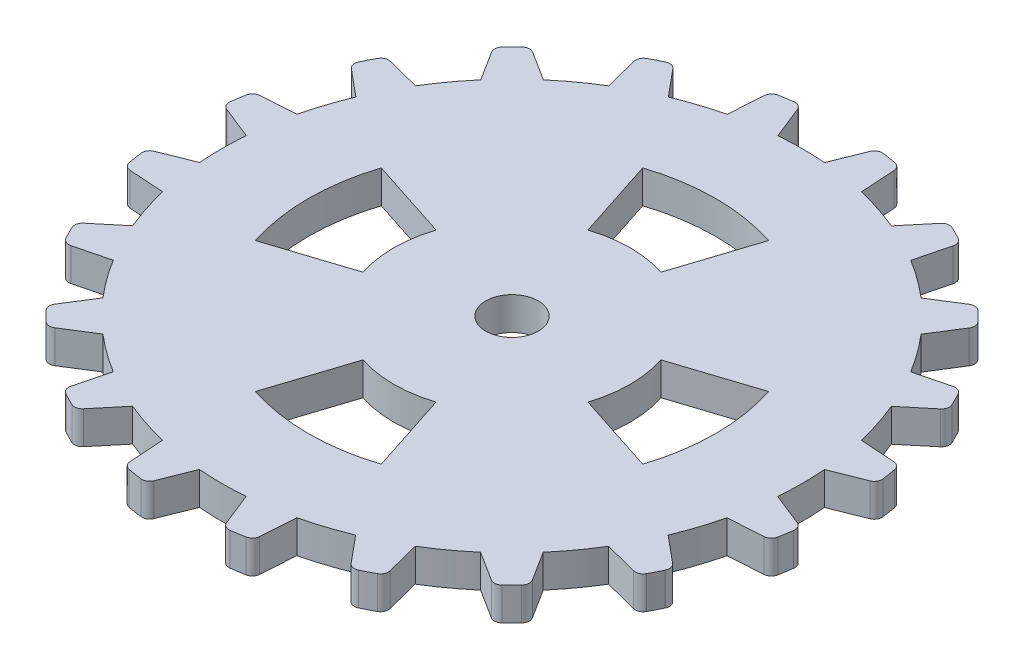
SolidWorks part; units mm, degrees
ref_plane "Front Plane" through (0, 0, 0) normal (0, 0, 1) x (1, 0, 0)
ref_plane "Top Plane" through (0, 0, 0) normal (0, 1, 0) x (1, 0, 0)
ref_plane "Right Plane" through (0, 0, 0) normal (1, 0, 0) x (0, 0, -1)
sketch "Sketch1" plane through (0, 0, 0) normal (0, 1, 0) x (1, 0, 0)
  line L0 (0, 0) -> (0, 28.8903) construction
  line L1 (-2.9264, 24.9115) -> (0, 0)
  line L2 (2.9395, 24.91) -> (0, 0)
  line L3 (-2.9264, 24.9115) -> (-1.7724, 22.0116)
  line L4 (2.9395, 24.91) -> (1.7839, 22.0106)
  line L5 (4.9149, 24.5966) -> (5.1163, 21.4819)
  line L6 (10.4932, 22.7824) -> (8.4983, 20.3821)
  line L7 (12.2751, 21.8739) -> (11.5042, 18.8495)
  line L8 (17.0198, 18.4248) -> (14.3807, 16.7584)
  line L9 (18.4337, 17.0101) -> (16.7659, 14.372)
  line L10 (21.8804, 12.2636) -> (18.8555, 11.4943)
  line L11 (22.7879, 10.4813) -> (20.3865, 8.4876)
  line L12 (24.5991, 4.902) -> (21.4846, 5.105)
  line L13 (24.9115, 2.9264) -> (22.0116, 1.7724)
  line L14 (24.91, -2.9395) -> (22.0106, -1.7839)
  line L15 (24.5966, -4.9149) -> (21.4819, -5.1163)
  line L16 (22.7824, -10.4932) -> (20.3821, -8.4983)
  line L17 (21.8739, -12.2751) -> (18.8495, -11.5042)
  line L18 (18.4248, -17.0198) -> (16.7584, -14.3807)
  line L19 (17.0101, -18.4337) -> (14.372, -16.7659)
  line L20 (12.2636, -21.8804) -> (11.4943, -18.8555)
  line L21 (10.4813, -22.7879) -> (8.4876, -20.3865)
  line L22 (4.902, -24.5991) -> (5.105, -21.4846)
  line L23 (2.9264, -24.9115) -> (1.7724, -22.0116)
  line L24 (-2.9395, -24.91) -> (-1.7839, -22.0106)
  line L25 (-4.9149, -24.5966) -> (-5.1163, -21.4819)
  line L26 (-10.4932, -22.7824) -> (-8.4983, -20.3821)
  line L27 (-12.2751, -21.8739) -> (-11.5042, -18.8495)
  line L28 (-17.0198, -18.4248) -> (-14.3807, -16.7584)
  line L29 (-18.4337, -17.0101) -> (-16.7659, -14.372)
  line L30 (-21.8804, -12.2636) -> (-18.8555, -11.4943)
  line L31 (-22.7879, -10.4813) -> (-20.3865, -8.4876)
  line L32 (-24.5991, -4.902) -> (-21.4846, -5.105)
  line L33 (-24.9115, -2.9264) -> (-22.0116, -1.7724)
  line L34 (-24.91, 2.9395) -> (-22.0106, 1.7839)
  line L35 (-24.5966, 4.9149) -> (-21.4819, 5.1163)
  line L36 (-22.7824, 10.4932) -> (-20.3821, 8.4983)
  line L37 (-21.8739, 12.2751) -> (-18.8495, 11.5042)
  line L38 (-18.4248, 17.0198) -> (-16.7584, 14.3807)
  line L39 (-17.0101, 18.4337) -> (-14.372, 16.7659)
  line L40 (-12.2636, 21.8804) -> (-11.4943, 18.8555)
  line L41 (-10.4813, 22.7879) -> (-8.4876, 20.3865)
  line L42 (-4.902, 24.5991) -> (-5.105, 21.4846)
  line L43 (4.7898, 14.7414) -> (2.7812, 8.5595)
  line L44 (-4.7898, 14.7414) -> (-2.7812, 8.5595)
  line L45 (14.7414, -4.7898) -> (8.5595, -2.7812)
  line L46 (14.7414, 4.7898) -> (8.5595, 2.7812)
  line L47 (-4.7898, -14.7414) -> (-2.7812, -8.5595)
  line L48 (4.7898, -14.7414) -> (2.7812, -8.5595)
  line L49 (-14.7414, 4.7898) -> (-8.5595, 2.7812)
  line L50 (-14.7414, -4.7898) -> (-8.5595, -2.7812)
  circle A0 centre (0, 0) radius 25.0828
  circle A1 centre (0, 0) radius 22.0828
  circle A2 centre (0, 0) radius 9
  circle A3 centre (0, 0) radius 15.5
  point P4 (-2.9264, 24.9115)
  point P7 (2.9395, 24.91)
  point P9 (-1.7724, 22.0116)
  point P13 (0, 22.0828)
  point P92 (0, 0)
  point P111 (0, 0)
  dimension "D1" = 50.1656
  dimension "D2" = 44.1656
  dimension "D8" = 18
  dimension "D9" = 31
  dimension "D3" = 13.43
  dimension "D4" = 6.7
  dimension "D5" = 15
  dimension "D6" = 15
  dimension "D10" = 18
  dimension "D11" = 18
  dimension "D7" = 20
  dimension "D12" = 4
extrude "Boss-Extrude1" add sketch "Sketch1" against normal blind 2.5 contours A1 L2 L1 | A1 L41 A0 L40 | A1 L1 A0 L42 | A1 L3 L1 | A1 L2 L4 | A1 L5 A0 L2 | A1 L7 A0 L6 | A1 L9 A0 L8 | A1 L11 A0 L10 | A1 L13 A0 L12 | L0 L2 A1 | L1 L0 A1 | A1 L15 A0 L14 | A1 L17 A0 L16 | A1 L19 A0 L18 | A1 L21 A0 L20 | A1 L23 A0 L22 | A1 L25 A0 L24 | A1 L27 A0 L26 | A1 L29 A0 L28 | A1 L31 A0 L30 | A1 L33 A0 L32 | A1 L39 A0 L38 | A1 L37 A0 L36 | A1 L35 A0 L34 | A3
fillet "Fillet1" radius 0.6 40 edges at (-10.4813, -1.25, -22.7879) (-17.0101, -1.25, -18.4337) (-24.91, -1.25, -2.9395) (-12.2636, -1.25, -21.8804) (-18.4248, -1.25, -17.0198) (-21.8739, -1.25, -12.2751) (-22.7824, -1.25, -10.4932) (-24.5966, -1.25, -4.9149) (-24.9115, -1.25, 2.9264) (-22.7879, -1.25, 10.4813) (-18.4337, -1.25, 17.0101) (-24.5991, -1.25, 4.902) (-21.8804, -1.25, 12.2636) (-17.0198, -1.25, 18.4248) (-12.2751, -1.25, 21.8739) (-10.4932, -1.25, 22.7824) (-4.9149, -1.25, 24.5966) (-2.9395, -1.25, 24.91) (2.9264, -1.25, 24.9115) (4.902, -1.25, 24.5991) (10.4813, -1.25, 22.7879) (12.2636, -1.25, 21.8804) (17.0101, -1.25, 18.4337) (18.4248, -1.25, 17.0198) (21.8739, -1.25, 12.2751) (22.7824, -1.25, 10.4932) (24.5966, -1.25, 4.9149) (24.91, -1.25, 2.9395) (24.9115, -1.25, -2.9264) (24.5991, -1.25, -4.902) (22.7879, -1.25, -10.4813) (21.8804, -1.25, -12.2636) (18.4337, -1.25, -17.0101) (17.0198, -1.25, -18.4248) (12.2751, -1.25, -21.8739) (10.4932, -1.25, -22.7824) (4.9149, -1.25, -24.5966) (2.9395, -1.25, -24.91) (-4.902, -1.25, -24.5991) (-2.9264, -1.25, -24.9115)
sketch "Sketch2" plane through (0, -2.5, 0) normal (0, -1, 0) x (1, 0, 0)
  line L0 (14.7414, -4.7898) -> (8.5595, -2.7812) construction
  line L1 (14.7414, 4.7898) -> (8.5595, 2.7812) construction
  line L2 (4.7898, 14.7414) -> (2.7812, 8.5595) construction
  line L3 (-4.7898, 14.7414) -> (-2.7812, 8.5595) construction
  line L4 (-14.7414, 4.7898) -> (-8.5595, 2.7812) construction
  line L5 (-14.7414, -4.7898) -> (-8.5595, -2.7812) construction
  line L6 (-4.7898, -14.7414) -> (-2.7812, -8.5595) construction
  line L7 (4.7898, -14.7414) -> (2.7812, -8.5595) construction
  line L8 (14.7414, -4.7898) -> (8.5595, -2.7812)
  line L9 (14.7414, 4.7898) -> (8.5595, 2.7812)
  line L10 (4.7898, 14.7414) -> (2.7812, 8.5595)
  line L11 (-4.7898, 14.7414) -> (-2.7812, 8.5595)
  line L12 (-14.7414, 4.7898) -> (-8.5595, 2.7812)
  line L13 (-14.7414, -4.7898) -> (-8.5595, -2.7812)
  line L14 (-4.7898, -14.7414) -> (-2.7812, -8.5595)
  line L15 (4.7898, -14.7414) -> (2.7812, -8.5595)
  circle A0 centre (0, 0) radius 9 construction
  circle A1 centre (0, 0) radius 15.5 construction
  circle A2 centre (0, 0) radius 9
  circle A3 centre (0, 0) radius 15.5
extrude "Cut-Extrude1" cut sketch "Sketch2" against normal through all contours L14 A3 L15 A2 | L8 A3 L9 A2 | L10 A3 L11 A2 | L12 A3 L13 A2
sketch "Sketch3" plane through (0, -2.5, 0) normal (0, -1, 0) x (1, 0, 0)
  circle A0 centre (0, 0) radius 2
  dimension "D1" = 4
extrude "Cut-Extrude2" cut sketch "Sketch3" against normal through all
